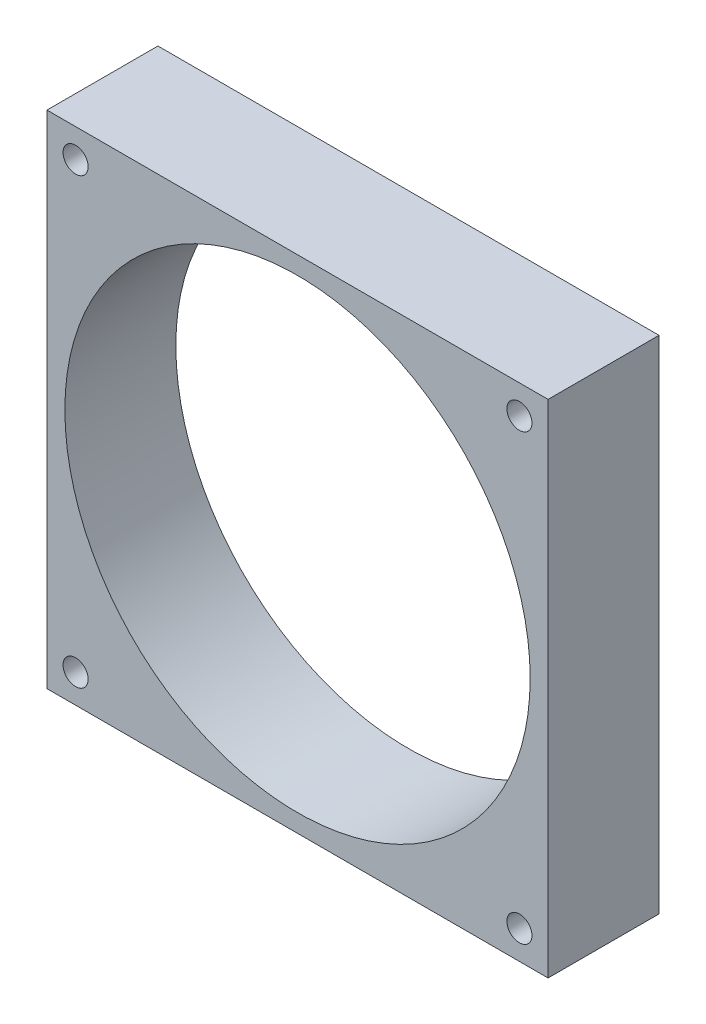
SolidWorks part; units mm, degrees
material "ABS"
ref_plane "Plano frontal" through (0, 0, 0) normal (0, 0, 1) x (1, 0, 0)
ref_plane "Plano superior" through (0, 0, 0) normal (0, 1, 0) x (1, 0, 0)
ref_plane "Plano direito" through (0, 0, 0) normal (1, 0, 0) x (0, 0, -1)
sketch "Esboço1" plane through (0, 0, 0) normal (0, 0, 1) x (1, 0, 0)
  line L1 (-35, 35) -> (35, 35)
  line L2 (-35, 35) -> (-35, -35)
  line L3 (-35, -35) -> (35, -35)
  line L4 (35, 35) -> (35, -35)
  line L5 (-35, 35) -> (35, -35) construction
  line L6 (-35, -35) -> (35, 35) construction
  circle A0 centre (-31, 31) radius 1.75
  circle A1 centre (0, 0) radius 32.5
  circle A2 centre (31, 31) radius 1.75
  circle A3 centre (0, 0) radius 32.5
  circle A4 centre (31, -31) radius 1.75
  circle A5 centre (0, 0) radius 32.5
  circle A6 centre (-31, -31) radius 1.75
  circle A7 centre (0, 0) radius 32.5
  point P0 (0, 0)
  point P22 (0, 0)
  dimension "D2" = 3.5
  dimension "D4" = 65
  dimension "D1" = 70
  dimension "D3" = 4
  dimension "D5" = 4
extrude "Ressalto-extrusão1" add sketch "Esboço1" along normal blind 15.5 contours L4 L1 L2 L3 A6 A4 A2 A1 A0
